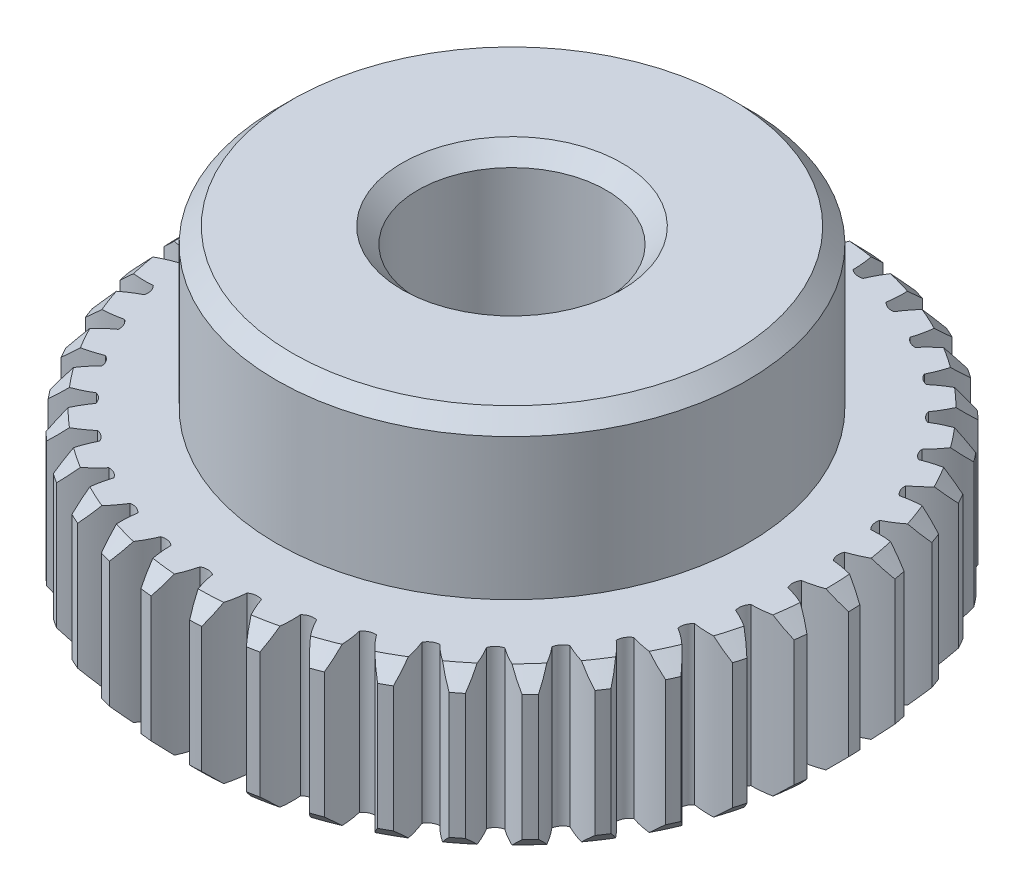
SolidWorks part; units mm, degrees
material "AISI 1045 鋼，冷拉"
ref_plane "Front Plane" through (0, 0, 0) normal (0, 0, 1) x (1, 0, 0)
ref_plane "Top Plane" through (0, 0, 0) normal (0, 1, 0) x (1, 0, 0)
ref_plane "Right Plane" through (0, 0, 0) normal (1, 0, 0) x (0, 0, -1)
sketch "草圖1" plane through (0, 0, 0) normal (0, 1, 0) x (1, 0, 0)
  circle A1 centre (0, 0) radius 21
  point P10 (0, 0)
  dimension "D2" = 42
extrude "填料-伸長1" add sketch "草圖1" along normal blind 10
sketch "草圖2" plane through (0, 10, 0) normal (0, 1, 0) x (1, 0, 0)
  line L0 (0, 8.1297) -> (0, -8.1297) construction
  line L1 (0, 20) -> (22.0146, 11.9873) construction
  line L2 (0, 20) -> (-6.4279, 17.6604) construction
  line L3 (0, 0) -> (0.8245, 20.9838) construction
  circle A1 centre (0, 0) radius 20 construction
  circle A2 centre (0, 0) radius 18.7939 construction
  arc A5 (0.3242, 18.756) -> (-0.4553, 20.9951) centre (-6.4279, 17.6604) ccw
  arc A6 (1.1484, 18.7236) -> (2.1012, 20.8946) centre (7.7937, 17.1017) cw
  arc A7 (2.1012, 20.8946) -> (-0.4553, 20.9951) centre (0, 0) ccw
  arc A8 (0.3242, 18.756) -> (1.1484, 18.7236) centre (0.765, 19.4711) ccw
  point P7 (0, 0)
  dimension "D1" = 40
  dimension "D2" = 0.84
  dimension "D4" = 6.8404
  dimension "D6" = 21
  dimension "D3" = 110
  dimension "D5" = 2.25
extrude "除料-伸長1" cut sketch "草圖2" against normal blind 10
chamfer "導角1" distance 1 angle 45 2 edges at (-0.8245, 0, 20.9838) (-0.8245, 10, 20.9838)
pattern_circular "環狀複製排列1" count 40 over 360 about axis through (0, 0, 0) along (0, 1, 0) of "除料-伸長1"
sketch "草圖4" plane through (0, 10, 0) normal (0, 1, 0) x (1, 0, 0)
  circle A0 centre (0, 0) radius 15
  dimension "D1" = 30
extrude "填料-伸長2" add sketch "草圖4" along normal blind 10
sketch "草圖3" plane through (0, 0, 0) normal (0, -1, 0) x (1, 0, 0)
  circle A0 centre (0, 0) radius 6
  dimension "D1" = 12
extrude "除料-伸長2" cut sketch "草圖3" against normal through all
chamfer "導角3" distance 1 angle 45 1 edges at (0, 20, 15)
chamfer "導角2" distance 1 angle 45 2 edges at (0, 0, -6) (0, 20, -6)
